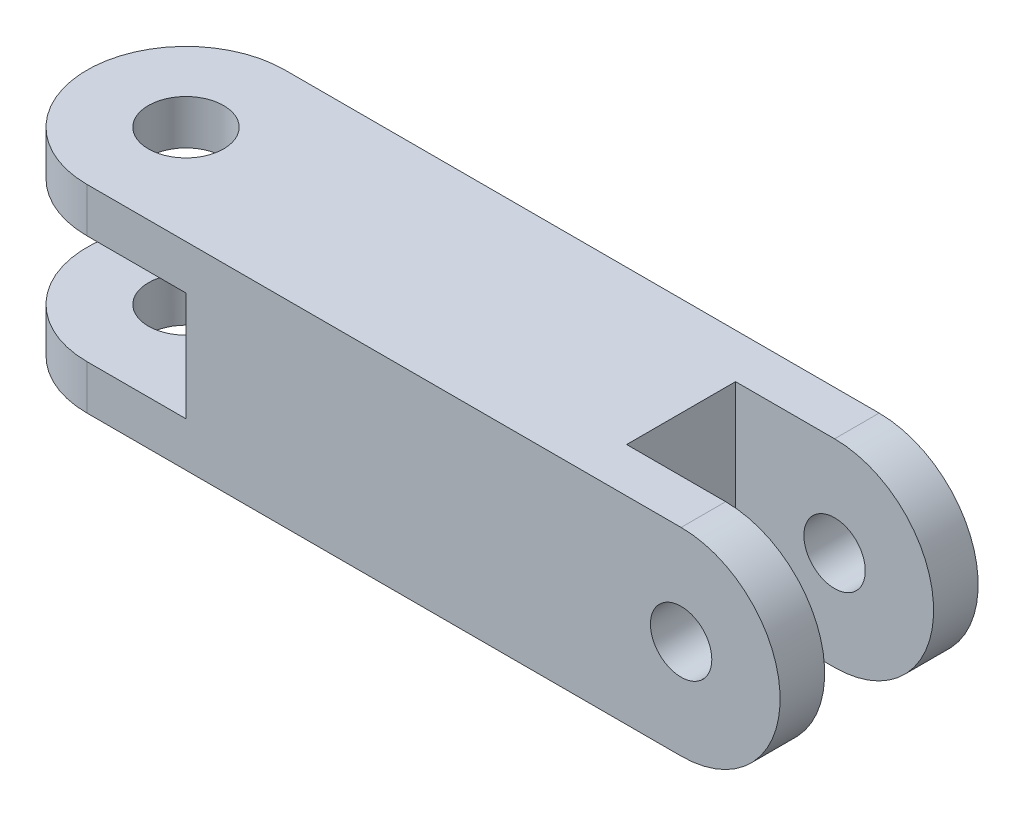
SolidWorks part; units mm, degrees
ref_plane "Front Plane" through (0, 0, 0) normal (0, 0, 1) x (1, 0, 0)
ref_plane "Top Plane" through (0, 0, 0) normal (0, 1, 0) x (1, 0, 0)
ref_plane "Right Plane" through (0, 0, 0) normal (1, 0, 0) x (0, 0, -1)
sketch "Sketch1" plane through (0, 0, 0) normal (0, 0, 1) x (1, 0, 0)
  line L1 (-24.0584, 4.1387) -> (5.9416, 4.1387)
  line L2 (-24.0584, 4.1387) -> (-24.0584, -5.8613)
  line L3 (-24.0584, -5.8613) -> (5.9416, -5.8613)
  line L4 (5.9416, 4.1387) -> (5.9416, -5.8613)
  dimension "D1" = 30
  dimension "D2" = 10
extrude "Boss-Extrude1" add sketch "Sketch1" along normal blind 10
sketch "Sketch2" plane through (0, 0, 10) normal (0, 0, 1) x (1, 0, 0)
  circle A0 centre (5.9416, -0.8613) radius 5
extrude "Boss-Extrude2" add sketch "Sketch2" against normal blind 2.25
sketch "Sketch3" plane through (0, 4.1387, 0) normal (0, 1, 0) x (1, 0, 0)
  line L0 (-24.0584, -10) -> (-24.0584, 0) construction
  line L1 (-24.0584, -10) -> (-24.0584, -5)
  line L2 (-24.0584, -5) -> (-29.0584, -5)
  arc A0 (-29.0584, -5) -> (-24.0584, -10) centre (-24.0584, -5) ccw
extrude "Boss-Extrude4" add sketch "Sketch3" against normal blind 2.25
ref_plane "Plane1" through (0, 0, 5) normal (0, 0, -1) x (-1, 0, 0)
mirror "Mirror1" about plane through (0, 0, 5) normal (0, 0, -1) of "Boss-Extrude4", "Boss-Extrude2"
ref_plane "Plane2" through (0, -0.8613, 0) normal (0, 1, 0) x (1, 0, 0)
mirror "Mirror3" about plane through (0, -0.8613, 0) normal (0, 1, 0) of "Boss-Extrude4"
mirror "Mirror4" about plane through (0, 0, 5) normal (0, 0, -1) of "Mirror3"
sketch "Sketch4" plane through (0, 4.1387, 0) normal (0, 1, 0) x (1, 0, 0)
  circle A2 centre (-24.0584, -5) radius 1.9
extrude "Cut-Extrude1" cut sketch "Sketch4" against normal blind 13.25
sketch "Sketch5" plane through (0, 0, 0) normal (0, 0, -1) x (-1, 0, 0)
  circle A2 centre (-5.9416, -0.8613) radius 1.55
  dimension "D1" = 3.1
extrude "Cut-Extrude2" cut sketch "Sketch5" against normal blind 13.25
sketch "Sketch6" plane through (0, 4.1387, 0) normal (0, 1, 0) x (1, 0, 0)
  line L0 (5.9416, -2.25) -> (0.9416, -2.25)
  line L1 (0.9416, -2.25) -> (0.9416, -7.75)
  line L2 (5.9416, -7.75) -> (0.9416, -7.75)
  line L3 (5.9416, -2.25) -> (5.9416, -7.75)
  dimension "D1" = 5
extrude "Cut-Extrude3" cut sketch "Sketch6" against normal blind 13.25
sketch "Sketch7" plane through (0, 0, 10) normal (0, 0, 1) x (1, 0, 0)
  line L0 (-24.0584, 1.8887) -> (-24.0584, -3.6113)
  line L1 (-24.0584, -3.6113) -> (-19.0584, -3.6113)
  line L2 (-19.0584, -3.6113) -> (-19.0584, 1.8887)
  line L3 (-19.0584, 1.8887) -> (-24.0584, 1.8887)
  dimension "D1" = 5
extrude "Cut-Extrude4" cut sketch "Sketch7" against normal blind 13.25
